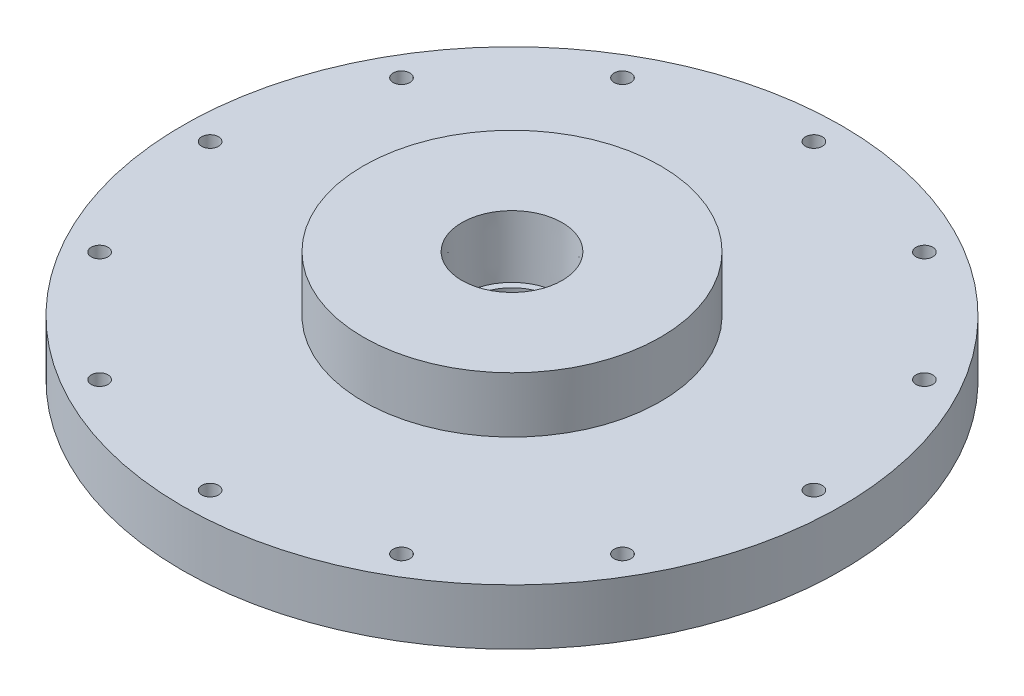
SolidWorks part; units mm, degrees
material "7075-T6 (SN)"
ref_plane "Front Plane" through (0, 0, 0) normal (0, 0, 1) x (1, 0, 0)
ref_plane "Top Plane" through (0, 0, 0) normal (0, 1, 0) x (1, 0, 0)
ref_plane "Right Plane" through (0, 0, 0) normal (1, 0, 0) x (0, 0, -1)
sketch "Sketch2" plane through (0, 0, 0) normal (0, 1, 0) x (1, 0, 0)
  circle A1 centre (0, 0) radius 25.4
  dimension "D1" = 50.8
extrude "Base Cylinder" add sketch "Sketch2" along normal blind 19.05
sketch "Sketch3" plane through (0, 0, 0) normal (0, -1, 0) x (1, 0, 0)
  circle A1 centre (0, 0) radius 56.3562
  dimension "D1" = 112.7125
extrude "Aft Flange" add sketch "Sketch3" against normal blind 9.525
sketch "Sketch For Bolt Holes" plane through (0, 0, 0) normal (0, -1, 0) x (1, 0, 0)
  circle A0 centre (-51.6255, 0) radius 1.5875
  circle A1 centre (-44.709, 25.8128) radius 1.5875
  circle A2 centre (-25.8128, 44.709) radius 1.5875
  circle A3 centre (0, 51.6255) radius 1.5875
  circle A4 centre (25.8127, 44.709) radius 1.5875
  circle A5 centre (44.709, 25.8128) radius 1.5875
  circle A6 centre (51.6255, 0) radius 1.5875
  circle A7 centre (44.709, -25.8127) radius 1.5875
  circle A8 centre (25.8128, -44.709) radius 1.5875
  circle A9 centre (0, -51.6255) radius 1.5875
  circle A10 centre (-25.8127, -44.709) radius 1.5875
  circle A11 centre (-44.709, -25.8128) radius 1.5875
  point P36 (0, 0)
  dimension "D2" = 3.175
  dimension "D1" = 51.6255
  dimension "D3" = 12
hole_wizard "Bolt Circle" positions "Sketch8" profile "Sketch9" hole size "#4-40" standard "ANSI Inch" end condition up to next
sketch "Sketch8" plane through (0, 0, 0) normal (0, -1, 0) x (-1, 0, 0)
  point P0 (-25.8127, -44.709)
  point P3 (-44.709, -25.8128)
  point P6 (-51.6255, 0)
  point P9 (-44.709, 25.8127)
  point P12 (-25.8128, 44.709)
  point P15 (0, 51.6255)
  point P18 (25.8127, 44.709)
  point P21 (44.709, 25.8128)
  point P24 (51.6255, 0)
  point P27 (44.709, -25.8128)
  point P30 (25.8128, -44.709)
  point P33 (0, -51.6255)
  point P36 (-25.8127, -44.709)
  point P38 (-44.709, -25.8128)
  point P40 (-51.6255, 0)
sketch "Sketch9" plane through (25.8127, 0, 44.709) normal (1, 0, 0) x (0, 0, -1)
  line L0 (0, 0) -> (0, 9.525)
  line L1 (0, 9.525) -> (1.4351, 9.525)
  line L2 (1.4351, 9.525) -> (1.4351, 0)
  line L5 (1.4351, 0) -> (0, 0)
  line L11 (0, -6.35) -> (0, 107.95) construction
  dimension "Thru Hole Dia." = 2.8702
  dimension "Thru Hole Depth" = 9.525
sketch "Dowel Hole Sketch" plane through (0, 0, 0) normal (0, -1, 0) x (1, 0, 0)
  line L0 (0, 0) -> (-51.6255, 0) construction
  line L1 (0, 0) -> (-49.8664, -13.3617) construction
  line L2 (0, 0) -> (0, -51.6255) construction
  line L3 (0, 0) -> (49.8664, 13.3617) construction
  circle A0 centre (0, 0) radius 51.6255
  circle A1 centre (-49.8664, -13.3617) radius 4.6172
  circle A2 centre (49.8664, 13.3617) radius 3.4532
  dimension "D1" = 15
ref_plane "Hoop Mid-Plane" through (0, 190.5, 0) normal (0, 1, 0) x (1, 0, 0)
sketch "Sketch15" plane through (0, 19.05, 0) normal (0, 1, 0) x (1, 0, 0)
  circle A0 centre (0, 0) radius 7.1106
hole_wizard "3/8 NPT Tapped Hole1" positions "Sketch16" profile "Sketch17" size "3/8" standard "ANSI Inch"
sketch "Sketch16" plane through (0, 19.05, 0) normal (0, 1, 0) x (1, 0, 0)
  point P0 (0, 0)
sketch "Sketch17" plane through (0, 19.05, 0) normal (1, 0, 0) x (0, 0, 1)
  line L0 (0, 0) -> (0, 21.8146)
  line L1 (7.1374, 17.526) -> (0, 21.8146)
  line L2 (-7.1374, 17.526) -> (0, 21.8146) construction
  line L3 (7.1374, 17.526) -> (7.1374, 10.414)
  line L4 (7.1374, 10.414) -> (8.2632, 10.414)
  line L5 (8.2632, 10.414) -> (8.575, 0)
  line L6 (-8.2632, 10.414) -> (-8.575, 0) construction
  line L7 (8.575, 0) -> (0, 0)
  line L8 (0, -6.35) -> (0, 107.95) construction
  line L11 (-7.1374, 10.414) -> (-8.2632, 10.414) construction
  dimension "Tap Drill Dia." = 14.2748
  dimension "Tap Drill Depth" = 17.526
  dimension "Thread Dia." = 17.15
  dimension "Thread Angle" = 3.43
  dimension "Thread Depth" = 10.414
  dimension "Drill Angle" = 118
